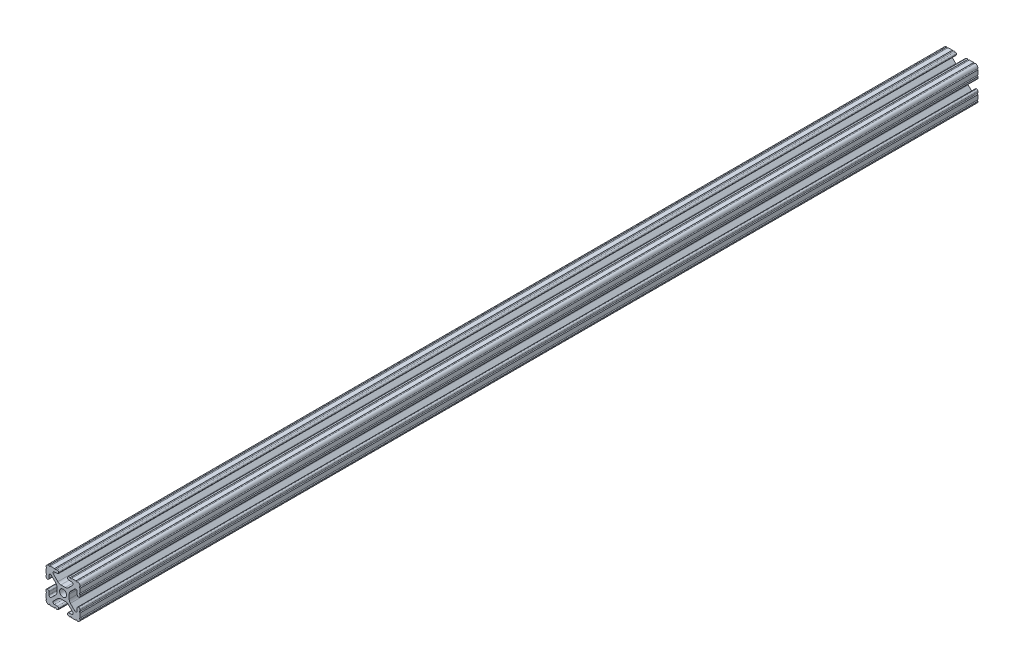
SolidWorks part; units mm, degrees
ref_plane "Front Plane" through (0, 0, 0) normal (0, 0, 1) x (1, 0, 0)
ref_plane "Top Plane" through (0, 0, 0) normal (0, 1, 0) x (1, 0, 0)
ref_plane "Right Plane" through (0, 0, 0) normal (1, 0, 0) x (0, 0, -1)
sketch "Sketch1" plane through (0, 0, 0) normal (0, 0, 1) x (1, 0, 0)
  line L88 (-7.1797, -8.6452) -> (-3.9523, -5.4237)
  line L89 (-1.7093, -4.4958) -> (1.7093, -4.4958)
  line L90 (3.9523, -5.4237) -> (7.1797, -8.6452)
  line L91 (6.4164, -10.4902) -> (4.2875, -10.4902)
  line L92 (3.2385, -11.5392) -> (3.2385, -11.651)
  line L93 (4.2875, -12.7) -> (5.3171, -12.7)
  line L94 (6.3331, -12.7) -> (9.5504, -12.7)
  line L95 (12.7, -9.5504) -> (12.7, -6.3331)
  line L96 (12.7, -5.3171) -> (12.7, -4.2875)
  line L97 (11.651, -3.2385) -> (11.5392, -3.2385)
  line L98 (10.4902, -4.2875) -> (10.4902, -6.4021)
  line L99 (8.7371, -7.1294) -> (5.441, -3.8408)
  line L100 (4.5085, -1.5932) -> (4.5085, 1.5932)
  line L101 (5.441, 3.8408) -> (8.7371, 7.1294)
  line L102 (10.4902, 6.4021) -> (10.4902, 4.2875)
  line L103 (11.5392, 3.2385) -> (11.651, 3.2385)
  line L104 (12.7, 4.2875) -> (12.7, 5.3171)
  line L105 (12.7, 6.3331) -> (12.7, 9.5504)
  line L106 (9.5504, 12.7) -> (6.3331, 12.7)
  line L107 (5.3171, 12.7) -> (4.2875, 12.7)
  line L108 (3.2385, 11.651) -> (3.2385, 11.5392)
  line L109 (4.2875, 10.4902) -> (6.4768, 10.4902)
  line L110 (7.207, 8.7244) -> (3.8983, 5.4232)
  line L111 (1.6558, 4.4958) -> (-1.6558, 4.4958)
  line L112 (-3.8983, 5.4232) -> (-7.207, 8.7244)
  line L113 (-6.4768, 10.4902) -> (-4.2875, 10.4902)
  line L114 (-3.2385, 11.5392) -> (-3.2385, 11.651)
  line L115 (-4.2875, 12.7) -> (-5.3171, 12.7)
  line L116 (-6.3331, 12.7) -> (-9.5504, 12.7)
  line L117 (-12.7, 9.5504) -> (-12.7, 6.3331)
  line L118 (-12.7, 5.3171) -> (-12.7, 4.2875)
  line L119 (-11.651, 3.2385) -> (-11.5392, 3.2385)
  line L120 (-10.4902, 4.2875) -> (-10.4902, 6.4021)
  line L121 (-8.7371, 7.1294) -> (-5.441, 3.8408)
  line L122 (-4.5085, 1.5932) -> (-4.5085, -1.5932)
  line L123 (-5.441, -3.8408) -> (-8.7371, -7.1294)
  line L124 (-10.4902, -6.4021) -> (-10.4902, -4.2875)
  line L125 (-11.5392, -3.2385) -> (-11.651, -3.2385)
  line L126 (-12.7, -4.2875) -> (-12.7, -5.3171)
  line L127 (-12.7, -6.3331) -> (-12.7, -9.5504)
  line L128 (-9.5504, -12.7) -> (-6.3331, -12.7)
  line L129 (-5.3171, -12.7) -> (-4.2875, -12.7)
  line L130 (-3.2385, -11.651) -> (-3.2385, -11.5392)
  line L131 (-4.2875, -10.4902) -> (-6.4164, -10.4902)
  circle A1 centre (0, 0) radius 2.6035
  arc A104 (-7.1797, -8.6452) -> (-6.4164, -10.4902) centre (-6.4164, -9.4098) ccw
  arc A105 (-1.7093, -4.4958) -> (-3.9523, -5.4237) centre (-1.7093, -7.6708) ccw
  arc A106 (3.9523, -5.4237) -> (1.7093, -4.4958) centre (1.7093, -7.6708) ccw
  arc A107 (6.4164, -10.4902) -> (7.1797, -8.6452) centre (6.4164, -9.4098) ccw
  arc A108 (4.2875, -10.4902) -> (3.2385, -11.5392) centre (4.2875, -11.5392) ccw
  arc A109 (3.2385, -11.651) -> (4.2875, -12.7) centre (4.2875, -11.651) ccw
  arc A110 (6.3331, -12.7) -> (5.3171, -12.7) centre (5.8251, -12.7) ccw
  arc A111 (10.5664, -12.6998) -> (9.5504, -12.7) centre (10.0584, -12.7) ccw
  arc A112 (10.5664, -12.6998) -> (12.6998, -10.5664) centre (10.5918, -10.5918) ccw
  arc A113 (12.7, -9.5504) -> (12.6998, -10.5664) centre (12.7, -10.0584) ccw
  arc A114 (12.7, -5.3171) -> (12.7, -6.3331) centre (12.7, -5.8251) ccw
  arc A115 (12.7, -4.2875) -> (11.651, -3.2385) centre (11.651, -4.2875) ccw
  arc A116 (11.5392, -3.2385) -> (10.4902, -4.2875) centre (11.5392, -4.2875) ccw
  arc A117 (8.7371, -7.1294) -> (10.4902, -6.4021) centre (9.4628, -6.4021) ccw
  arc A118 (4.5085, -1.5932) -> (5.441, -3.8408) centre (7.6835, -1.5932) ccw
  arc A119 (5.441, 3.8408) -> (4.5085, 1.5932) centre (7.6835, 1.5932) ccw
  arc A120 (10.4902, 6.4021) -> (8.7371, 7.1294) centre (9.4628, 6.4021) ccw
  arc A121 (10.4902, 4.2875) -> (11.5392, 3.2385) centre (11.5392, 4.2875) ccw
  arc A122 (11.651, 3.2385) -> (12.7, 4.2875) centre (11.651, 4.2875) ccw
  arc A123 (12.7, 6.3331) -> (12.7, 5.3171) centre (12.7, 5.8251) ccw
  arc A124 (12.6998, 10.5664) -> (12.7, 9.5504) centre (12.7, 10.0584) ccw
  arc A125 (12.6998, 10.5664) -> (10.5664, 12.6998) centre (10.5918, 10.5918) ccw
  arc A126 (9.5504, 12.7) -> (10.5664, 12.6998) centre (10.0584, 12.7) ccw
  arc A127 (5.3171, 12.7) -> (6.3331, 12.7) centre (5.8251, 12.7) ccw
  arc A128 (4.2875, 12.7) -> (3.2385, 11.651) centre (4.2875, 11.651) ccw
  arc A129 (3.2385, 11.5392) -> (4.2875, 10.4902) centre (4.2875, 11.5392) ccw
  arc A130 (7.207, 8.7244) -> (6.4768, 10.4902) centre (6.4768, 9.4563) ccw
  arc A131 (1.6558, 4.4958) -> (3.8983, 5.4232) centre (1.6558, 7.6708) ccw
  arc A132 (-3.8983, 5.4232) -> (-1.6558, 4.4958) centre (-1.6558, 7.6708) ccw
  arc A133 (-6.4768, 10.4902) -> (-7.207, 8.7244) centre (-6.4768, 9.4563) ccw
  arc A134 (-4.2875, 10.4902) -> (-3.2385, 11.5392) centre (-4.2875, 11.5392) ccw
  arc A135 (-3.2385, 11.651) -> (-4.2875, 12.7) centre (-4.2875, 11.651) ccw
  arc A136 (-6.3331, 12.7) -> (-5.3171, 12.7) centre (-5.8251, 12.7) ccw
  arc A137 (-10.5664, 12.6998) -> (-9.5504, 12.7) centre (-10.0584, 12.7) ccw
  arc A138 (-10.5664, 12.6998) -> (-12.6998, 10.5664) centre (-10.5918, 10.5918) ccw
  arc A139 (-12.7, 9.5504) -> (-12.6998, 10.5664) centre (-12.7, 10.0584) ccw
  arc A140 (-12.7, 5.3171) -> (-12.7, 6.3331) centre (-12.7, 5.8251) ccw
  arc A141 (-12.7, 4.2875) -> (-11.651, 3.2385) centre (-11.651, 4.2875) ccw
  arc A142 (-11.5392, 3.2385) -> (-10.4902, 4.2875) centre (-11.5392, 4.2875) ccw
  arc A143 (-8.7371, 7.1294) -> (-10.4902, 6.4021) centre (-9.4628, 6.4021) ccw
  arc A144 (-4.5085, 1.5932) -> (-5.441, 3.8408) centre (-7.6835, 1.5932) ccw
  arc A145 (-5.441, -3.8408) -> (-4.5085, -1.5932) centre (-7.6835, -1.5932) ccw
  arc A146 (-10.4902, -6.4021) -> (-8.7371, -7.1294) centre (-9.4628, -6.4021) ccw
  arc A147 (-10.4902, -4.2875) -> (-11.5392, -3.2385) centre (-11.5392, -4.2875) ccw
  arc A148 (-11.651, -3.2385) -> (-12.7, -4.2875) centre (-11.651, -4.2875) ccw
  arc A149 (-12.7, -6.3331) -> (-12.7, -5.3171) centre (-12.7, -5.8251) ccw
  arc A150 (-12.6998, -10.5664) -> (-12.7, -9.5504) centre (-12.7, -10.0584) ccw
  arc A151 (-12.6998, -10.5664) -> (-10.5664, -12.6998) centre (-10.5918, -10.5918) ccw
  arc A152 (-9.5504, -12.7) -> (-10.5664, -12.6998) centre (-10.0584, -12.7) ccw
  arc A153 (-5.3171, -12.7) -> (-6.3331, -12.7) centre (-5.8251, -12.7) ccw
  arc A154 (-4.2875, -12.7) -> (-3.2385, -11.651) centre (-4.2875, -11.651) ccw
  arc A155 (-3.2385, -11.5392) -> (-4.2875, -10.4902) centre (-4.2875, -11.5392) ccw
extrude "Boss-Extrude1" add sketch "Sketch1" along normal mid plane 1828.8
sketch "Sketch2" plane through (12.7, 0, 0) normal (1, 0, 0) x (0, 0, -1)
  line L0 (-842.1091, -105.1) -> (-842.1091, 28.4774) construction
  line L1 (-174.9218, -42.647) -> (-174.9218, 41.3341) construction
  line L2 (-842.1091, 16.7947) -> (-842.1091, -17.9661)
  line L3 (-842.1091, -17.9661) -> (-918.4573, -17.9661)
  line L4 (-918.4573, -17.9661) -> (-918.4573, 16.7947)
  line L5 (-918.4573, 16.7947) -> (-842.1091, 16.7947)
  line L6 (-174.9218, -17.9661) -> (-174.9218, 18.2032)
  line L7 (-174.9218, 18.2032) -> (925.0572, 18.2032)
  line L8 (925.0572, 18.2032) -> (925.0572, -17.9661)
  line L9 (925.0572, -17.9661) -> (-174.9218, -17.9661)
  circle A0 centre (-852.7591, -105.1) radius 10.65 construction
  arc A1 (-164.2718, -31.997) -> (-164.2718, -53.297) centre (-164.2718, -42.647) ccw construction
extrude "Cut-Extrude1" cut sketch "Sketch2" against normal blind 27.432
